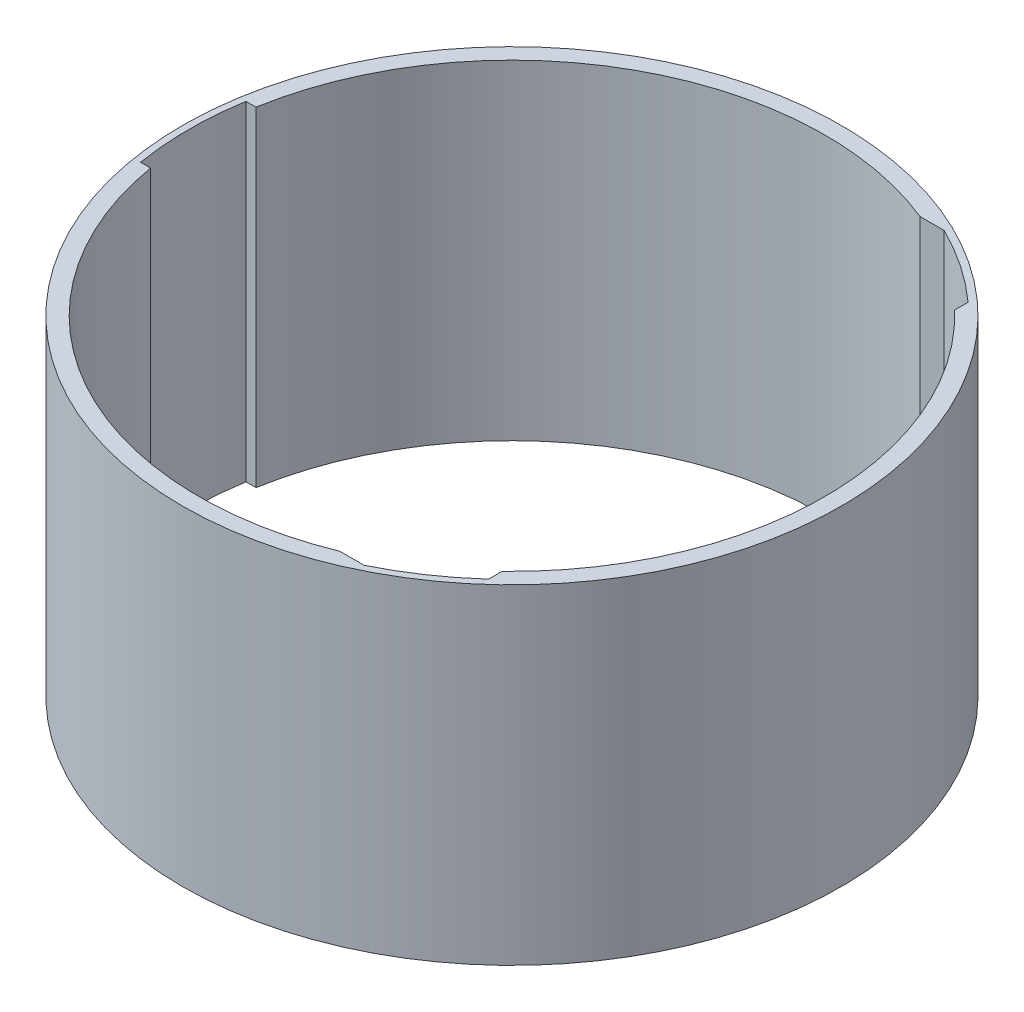
SolidWorks part; units mm, degrees
ref_plane "Front Plane" through (0, 0, 0) normal (0, 0, 1) x (1, 0, 0)
ref_plane "Top Plane" through (0, 0, 0) normal (0, 1, 0) x (1, 0, 0)
ref_plane "Right Plane" through (0, 0, 0) normal (1, 0, 0) x (0, 0, -1)
sketch "Sketch1" plane through (0, 0, 0) normal (0, 1, 0) x (1, 0, 0)
  circle A0 centre (0, 0) radius 100
  circle A1 centre (0, 0) radius 95
  dimension "D1" = 200
  dimension "D2" = 5
extrude "Boss-Extrude1" add sketch "Sketch1" along normal blind 100
sketch "Sketch2" plane through (0, 100, 0) normal (0, 1, 0) x (1, 0, 0)
  line L0 (43.1541, 87.9871) -> (35.6568, 87.9871)
  line L1 (-110.5, -16) -> (-85.5, -16)
  line L2 (-110.5, -16) -> (-110.5, 16)
  line L3 (-110.5, 16) -> (-85.5, 16)
  line L4 (-85.5, -16) -> (-85.5, 16)
  line L5 (-110.5, -16) -> (-85.5, 16) construction
  line L6 (-110.5, 16) -> (-85.5, -16) construction
  line L7 (35.6568, 87.9871) -> (35.6568, 65.9871)
  line L8 (35.6568, 65.9871) -> (65.6568, 65.9871)
  line L9 (65.6568, 65.9871) -> (65.6568, 72.7542)
  line L10 (43.1541, -87.9871) -> (35.6568, -87.9871)
  line L11 (35.6568, -87.9871) -> (35.6568, -65.9871)
  line L12 (35.6568, -65.9871) -> (65.6568, -65.9871)
  line L13 (65.6568, -65.9871) -> (65.6568, -72.7542)
  circle A2 centre (0, 0) radius 98
  circle A3 centre (0, 0) radius 98
  point P0 (-98, 0)
  point P17 (35.677, 66.7282)
  point P19 (0, 0)
  point P20 (0, 0)
  circle M13 centre (0, 0) radius 95
  dimension "D2" = 25
  dimension "D3" = 32
  dimension "D4" = 22
  dimension "D5" = 30
  dimension "D1" = 2
extrude "Cut-Extrude1" cut sketch "Sketch2" against normal through all contours L9 A3 L0 M13 | L10 A3 L13 M13 | L3 A3 L1 M13
